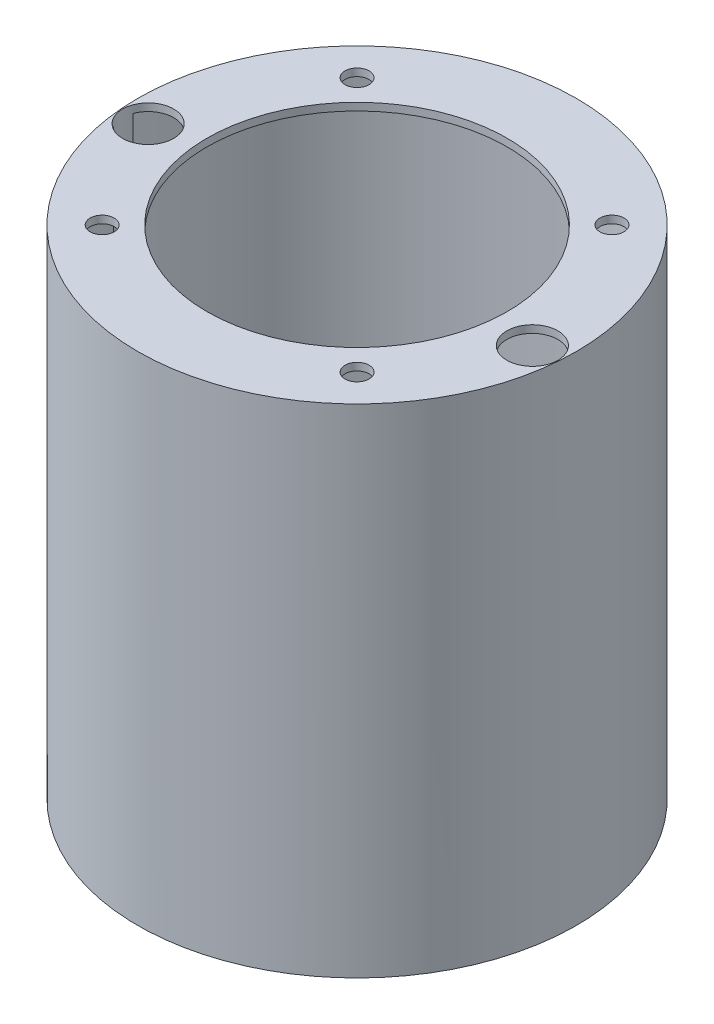
SolidWorks part; units mm, degrees
ref_plane "Front Plane" through (0, 0, 0) normal (0, 0, 1) x (1, 0, 0)
ref_plane "Top Plane" through (0, 0, 0) normal (0, 1, 0) x (1, 0, 0)
ref_plane "Right Plane" through (0, 0, 0) normal (1, 0, 0) x (0, 0, -1)
sketch "Sketch1" plane through (0, 0, 0) normal (0, 1, 0) x (1, 0, 0)
  circle A0 centre (0, 0) radius 92.71
  circle A1 centre (0, 0) radius 63.5
  dimension "D1" = 127
  dimension "D2" = 185.42
extrude "Top Ring " add sketch "Sketch1" along normal blind 3.175
sketch "Sketch2" plane through (0, 0, 0) normal (0, -1, 0) x (1, 0, 0)
  circle A0 centre (0, 0) radius 92.71
  circle A1 centre (0, 0) radius 91.44
  dimension "D1" = 185.42
  dimension "D2" = 1.27
extrude "Cylindrical extenstion " add sketch "Sketch2" along normal blind 207.01
sketch "Sketch3" plane through (0, 3.175, 0) normal (0, 1, 0) x (1, 0, 0)
  line L0 (0, 0) -> (81.534, 0) construction
  line L1 (0, 0) -> (81.2237, -7.1062) construction
  circle A0 centre (0, 0) radius 81.534 construction
  circle A1 centre (81.2237, -7.1062) radius 10.795
  dimension "D1" = 163.068
  dimension "D2" = 21.59
  dimension "D3" = 5
extrude "Nose Cone Ejection Charge Hole" cut sketch "Sketch3" against normal up to surface (210.185 mm away) up to face at (0, -207.01, -92.71)
mirror "Nose Cone Ejection Charge Mirror " about plane through (0, 0, 0) normal (1, 0, 0) of "Nose Cone Ejection Charge Hole"
sketch "Sketch4" plane through (0, 3.175, 0) normal (0, 1, 0) x (1, 0, 0)
  line L0 (0, 0) -> (76.2, 0) construction
  line L1 (53.8815, -53.8815) -> (0, 0) construction
  circle A0 centre (0, 0) radius 76.2 construction
  circle A1 centre (53.8815, -53.8815) radius 5.08
  circle A2 centre (-53.8815, -53.8815) radius 5.08
  circle A3 centre (-53.8815, 53.8815) radius 5.08
  circle A4 centre (53.8815, 53.8815) radius 5.08
  point P15 (0, 0)
  dimension "D1" = 45
  dimension "D2" = 10.16
  dimension "D3" = 152.4
  dimension "D4" = 4
extrude "Cut-Extrude1" cut sketch "Sketch4" against normal up to surface (3.175 mm away) up to face at (0, 0, 3.0827)
